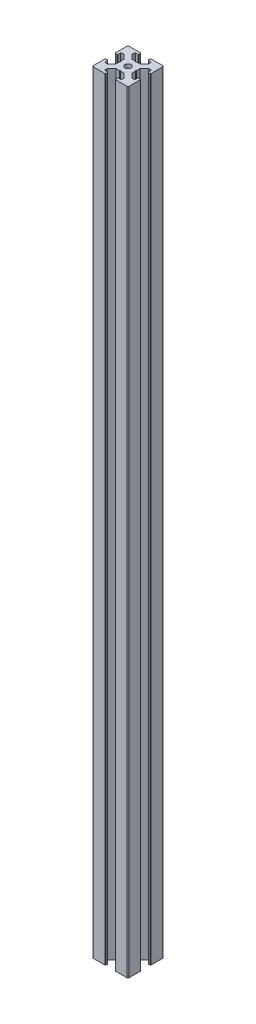
SolidWorks part; units mm, degrees
ref_plane "Front Plane" through (0, 0, 0) normal (0, 0, 1) x (1, 0, 0)
ref_plane "Top Plane" through (0, 0, 0) normal (0, 1, 0) x (1, 0, 0)
ref_plane "Right Plane" through (0, 0, 0) normal (1, 0, 0) x (0, 0, -1)
sketch "Sketch3" plane through (0, 0, 0) normal (0, 1, 0) x (1, 0, 0)
  line L0 (11, 30) -> (11, 27.75)
  line L1 (0, 0) -> (30, 0)
  line L2 (0, 0) -> (0, 30)
  line L3 (0, 30) -> (30, 30)
  line L4 (30, 0) -> (30, 30)
  line L5 (11, 27.75) -> (8, 27.75)
  line L6 (8, 27.75) -> (8, 25.5)
  line L7 (8, 25.5) -> (11.5, 21.75)
  line L8 (11.5, 21.75) -> (18.5, 21.75)
  line L9 (18.5, 21.75) -> (22, 25.5)
  line L10 (22, 25.5) -> (22, 27.75)
  line L11 (22, 27.75) -> (19, 27.75)
  line L12 (19, 27.75) -> (19, 30)
  line L13 (19, 30) -> (11, 30)
  line L14 (14.5, 21.75) -> (15, 21.25)
  line L15 (15, 21.25) -> (15.5, 21.75)
  line L16 (15.5, 21.75) -> (14.5, 21.75)
  line L17 (19, 29.5) -> (19, 30)
  line L18 (19.5, 30) -> (19, 30)
  line L19 (11, 29.5) -> (11, 30)
  line L20 (10.5, 30) -> (11, 30)
  line L21 (0, 19) -> (2.25, 19)
  line L22 (2.25, 19) -> (2.25, 22)
  line L23 (2.25, 22) -> (4.5, 22)
  line L24 (4.5, 22) -> (8.25, 18.5)
  line L25 (8.25, 18.5) -> (8.25, 11.5)
  line L26 (8.25, 11.5) -> (4.5, 8)
  line L27 (4.5, 8) -> (2.25, 8)
  line L28 (2.25, 8) -> (2.25, 11)
  line L29 (2.25, 11) -> (0, 11)
  line L30 (0, 11) -> (0, 19)
  line L31 (8.25, 15.5) -> (8.25, 14.5)
  line L32 (8.25, 14.5) -> (8.75, 15)
  line L33 (8.75, 15) -> (8.25, 15.5)
  line L34 (0.5, 19) -> (0, 19)
  line L35 (0, 19.5) -> (0, 19)
  line L36 (0, 10.5) -> (0, 11)
  line L37 (0.5, 11) -> (0, 11)
  line L38 (15, 30) -> (15, 0) construction
  line L39 (30, 15) -> (0, 15) construction
  line L40 (15, 8.75) -> (15.5, 8.25)
  line L41 (14.5, 8.25) -> (15, 8.75)
  line L42 (15.5, 8.25) -> (14.5, 8.25)
  line L43 (19.5, 0) -> (19, 0)
  line L44 (19, 0.5) -> (19, 0)
  line L45 (10.5, 0) -> (11, 0)
  line L46 (11, 0.5) -> (11, 0)
  line L47 (19, 2.25) -> (19, 0)
  line L48 (22, 2.25) -> (19, 2.25)
  line L49 (22, 4.5) -> (22, 2.25)
  line L50 (18.5, 8.25) -> (22, 4.5)
  line L51 (11.5, 8.25) -> (18.5, 8.25)
  line L52 (8, 4.5) -> (11.5, 8.25)
  line L53 (8, 2.25) -> (8, 4.5)
  line L54 (11, 2.25) -> (8, 2.25)
  line L55 (11, 0) -> (11, 2.25)
  line L56 (19, 0) -> (11, 0)
  line L57 (21.75, 14.5) -> (21.25, 15)
  line L58 (21.75, 15.5) -> (21.75, 14.5)
  line L59 (21.25, 15) -> (21.75, 15.5)
  line L60 (29.5, 11) -> (30, 11)
  line L61 (30, 10.5) -> (30, 11)
  line L62 (30, 19.5) -> (30, 19)
  line L63 (29.5, 19) -> (30, 19)
  line L64 (27.75, 11) -> (30, 11)
  line L65 (27.75, 8) -> (27.75, 11)
  line L66 (25.5, 8) -> (27.75, 8)
  line L67 (21.75, 11.5) -> (25.5, 8)
  line L68 (21.75, 18.5) -> (21.75, 11.5)
  line L69 (25.5, 22) -> (21.75, 18.5)
  line L70 (27.75, 22) -> (25.5, 22)
  line L71 (27.75, 19) -> (27.75, 22)
  line L72 (30, 19) -> (27.75, 19)
  line L73 (30, 11) -> (30, 19)
  arc A0 (19.5, 30) -> (19, 29.5) centre (19, 30) cw
  arc A1 (10.5, 30) -> (11, 29.5) centre (11, 30) ccw
  arc A2 (0.5, 19) -> (0, 19.5) centre (0, 19) ccw
  arc A3 (0.5, 11) -> (0, 10.5) centre (0, 11) cw
  arc A4 (19.5, 0) -> (19, 0.5) centre (19, 0) ccw
  arc A5 (10.5, 0) -> (11, 0.5) centre (11, 0) cw
  arc A6 (29.5, 11) -> (30, 10.5) centre (30, 11) ccw
  arc A7 (29.5, 19) -> (30, 19.5) centre (30, 19) cw
  point P7 (15, 21.75)
  point P16 (15, 30)
  point P26 (8.25, 15)
  point P35 (0, 15)
  dimension "D16" = 0.5
  dimension "D17" = 0.5
  dimension "D28" = 0.5
  dimension "D29" = 0.5
  dimension "D1" = 30
  dimension "D2" = 30
  dimension "D3" = 11
  dimension "D4" = 11
  dimension "D5" = 2.25
  dimension "D6" = 2.25
  dimension "D7" = 3
  dimension "D8" = 3
  dimension "D9" = 2.25
  dimension "D10" = 2.25
  dimension "D11" = 7
  dimension "D12" = 8.25
  dimension "D13" = 0.5
  dimension "D14" = 0.5
  dimension "D15" = 0.5
  dimension "D18" = 11
  dimension "D19" = 11
  dimension "D20" = 2.25
  dimension "D21" = 2.25
  dimension "D22" = 3
  dimension "D23" = 7
  dimension "D24" = 8.25
  dimension "D25" = 0.5
  dimension "D26" = 0.5
  dimension "D27" = 0.5
extrude "Boss-Extrude1" add sketch "Sketch3" along normal blind 649 contours L72 A7 L4 L3 A0 L12 L11 L10 L9 L8 L15 L14 L7 L6 L5 L0 A1 L2 A2 L21 L22 L23 L24 L25 L33 L32 L26 L27 L28 L29 A3 L1 A5 L55 L54 L53 L52 L51 L41 L40 L50 L49 L48 L47 A4
fillet "Fillet1" radius 1 4 edges at (0, 324.5, 0) (30, 324.5, 0) (30, 324.5, -30) (0, 324.5, -30)
sketch "Sketch4" plane through (0, 649, 0) normal (0, 1, 0) x (1, 0, 0)
  line L0 (18.5, 21.75) -> (8.25, 11.5) construction
  line L1 (21.75, 18.5) -> (11.5, 8.25) construction
  line L2 (15.5, 21.75) -> (21.75, 15.5) construction
  line L9 (8.25, 14.5) -> (14.5, 8.25) construction
  line L10 (8.25, 15.5) -> (14.5, 21.75) construction
  line L11 (21.75, 14.5) -> (15.5, 8.25) construction
  line L12 (11.5, 21.75) -> (21.75, 11.5) construction
  line L13 (8.25, 18.5) -> (18.5, 8.25) construction
  line L20 (30, 15) -> (0, 15) construction
  circle A0 centre (15, 15) radius 2.5
  dimension "D1" = 5
extrude "Cut-Extrude1" cut sketch "Sketch4" against normal through all
fillet "Fillet2" radius 0.5 24 edges at (2.25, 324.5, -22) (2.25, 324.5, -19) (8.25, 324.5, -15.5) (8.25, 324.5, -14.5) (2.25, 324.5, -11) (2.25, 324.5, -8) (8, 324.5, -2.25) (11, 324.5, -2.25) (14.5, 324.5, -8.25) (15.5, 324.5, -8.25) (19, 324.5, -2.25) (22, 324.5, -2.25) (27.75, 324.5, -8) (27.75, 324.5, -11) (27.75, 324.5, -19) (27.75, 324.5, -22) (21.75, 324.5, -14.5) (21.75, 324.5, -15.5) (15.5, 324.5, -21.75) (14.5, 324.5, -21.75) (22, 324.5, -27.75) (19, 324.5, -27.75) (11, 324.5, -27.75) (8, 324.5, -27.75)
